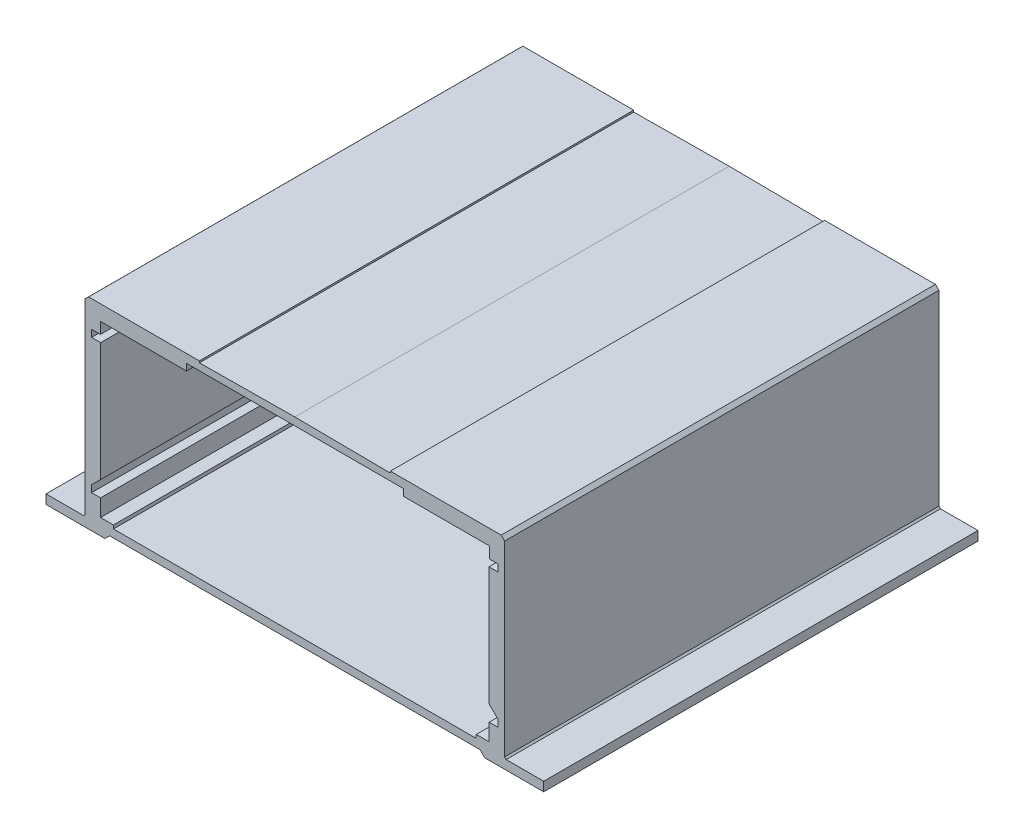
SolidWorks part; units mm, degrees
ref_plane "Front Plane" through (0, 0, 0) normal (0, 0, 1) x (1, 0, 0)
ref_plane "Top Plane" through (0, 0, 0) normal (0, 1, 0) x (1, 0, 0)
ref_plane "Right Plane" through (0, 0, 0) normal (1, 0, 0) x (0, 0, -1)
sketch "Sketch1" plane through (0, 0, 0) normal (0, 0, 1) x (1, 0, 0)
  line L0 (42.6405, 0) -> (-42.6405, 0)
  line L1 (0, -8.4215) -> (0, 52.7353) construction
  line L2 (-42.6405, 0) -> (-43.7433, -1.0848)
  line L3 (-43.7433, -1.0848) -> (-57.3, -1.0848)
  line L4 (-57.3, -1.0848) -> (-57.3, 1.0339)
  line L5 (-57.3, 1.0339) -> (-48.6568, 1.0339)
  line L6 (-48.6568, 1.0339) -> (-48.3, 1.3849)
  line L7 (-48.3, 1.3849) -> (-48.3, 44.4272)
  line L8 (-48.3, 44.4272) -> (-47.4989, 45.2152)
  line L9 (-47.4989, 45.2152) -> (-21.9882, 45.2152)
  line L10 (-21.9882, 45.2152) -> (-21.9882, 44.8245)
  line L11 (-21.9882, 44.8245) -> (0, 45.0232)
  line L12 (0, 45.0232) -> (0, 43.2456)
  line L13 (24.9739, 43.2456) -> (-24.9739, 43.2456)
  line L14 (-24.9739, 43.2456) -> (-24.9739, 41.7059)
  line L15 (-24.9739, 41.7059) -> (-44.7677, 41.7059)
  line L16 (-44.7677, 41.7059) -> (-44.7677, 39.095)
  line L17 (-44.7677, 39.095) -> (-46.8, 39.095)
  line L18 (-46.8, 39.095) -> (-46.8, 37.495)
  line L19 (-46.8, 37.495) -> (-44.7, 37.495)
  line L20 (-44.7, 37.495) -> (-44.7, 10.1883)
  line L21 (-44.7, 10.1883) -> (-46.8, 8.1227)
  line L22 (-46.8, 8.1227) -> (-46.8, 6.5227)
  line L23 (-46.8, 6.5227) -> (-44.7344, 6.5227)
  line L24 (-44.7344, 6.5227) -> (-44.7344, 2.603)
  line L25 (-44.7344, 2.603) -> (-41.7678, 2.603)
  line L26 (-41.7678, 2.603) -> (-41.7678, 1.8059)
  line L27 (-41.7678, 1.8059) -> (41.7678, 1.8059)
  line L28 (0, 1.8059) -> (0, 0)
  line L29 (41.7678, 2.603) -> (41.7678, 1.8059)
  line L30 (44.7344, 2.603) -> (41.7678, 2.603)
  line L31 (44.7344, 6.5227) -> (44.7344, 2.603)
  line L32 (46.8, 6.5227) -> (44.7344, 6.5227)
  line L33 (46.8, 8.1227) -> (46.8, 6.5227)
  line L34 (44.7, 10.1883) -> (46.8, 8.1227)
  line L35 (44.7, 37.495) -> (44.7, 10.1883)
  line L36 (46.8, 37.495) -> (44.7, 37.495)
  line L37 (46.8, 39.095) -> (46.8, 37.495)
  line L38 (44.7677, 39.095) -> (46.8, 39.095)
  line L39 (44.7677, 41.7059) -> (44.7677, 39.095)
  line L40 (24.9739, 41.7059) -> (44.7677, 41.7059)
  line L41 (24.9739, 43.2456) -> (24.9739, 41.7059)
  line L42 (21.9882, 44.8245) -> (0, 45.0232)
  line L43 (21.9882, 45.2152) -> (21.9882, 44.8245)
  line L44 (47.4989, 45.2152) -> (21.9882, 45.2152)
  line L45 (48.3, 44.4272) -> (47.4989, 45.2152)
  line L46 (48.3, 1.3849) -> (48.3, 44.4272)
  line L47 (48.6568, 1.0339) -> (48.3, 1.3849)
  line L48 (57.3, 1.0339) -> (48.6568, 1.0339)
  line L49 (57.3, -1.0848) -> (57.3, 1.0339)
  line L50 (43.7433, -1.0848) -> (57.3, -1.0848)
  line L51 (42.6405, 0) -> (43.7433, -1.0848)
  point P14 (-46.8, 38.295)
  dimension "D1" = 1.6
  dimension "D2" = 1.6
  dimension "D3" = 39.9
  dimension "D4" = 114.6
  dimension "D5" = 96.6
  dimension "D6" = 93.6
  dimension "D7" = 46.3
  dimension "D8" = 93.6
  dimension "D9" = 89.4
extrude "Boss-Extrude1" add sketch "Sketch1" along normal blind 100 contours L28 L27 L26 L25 L24 L23 L22 L21 L20 L19 L18 L17 L16 L15 L14 L13 L12 L11 L10 L9 L8 L7 L6 L5 L4 L3 L2 L0 | L0 L51 L50 L49 L48 L47 L46 L45 L44 L43 L42 L12 L13 L41 L40 L39 L38 L37 L36 L35 L34 L33 L32 L31 L30 L29 L27 L28
